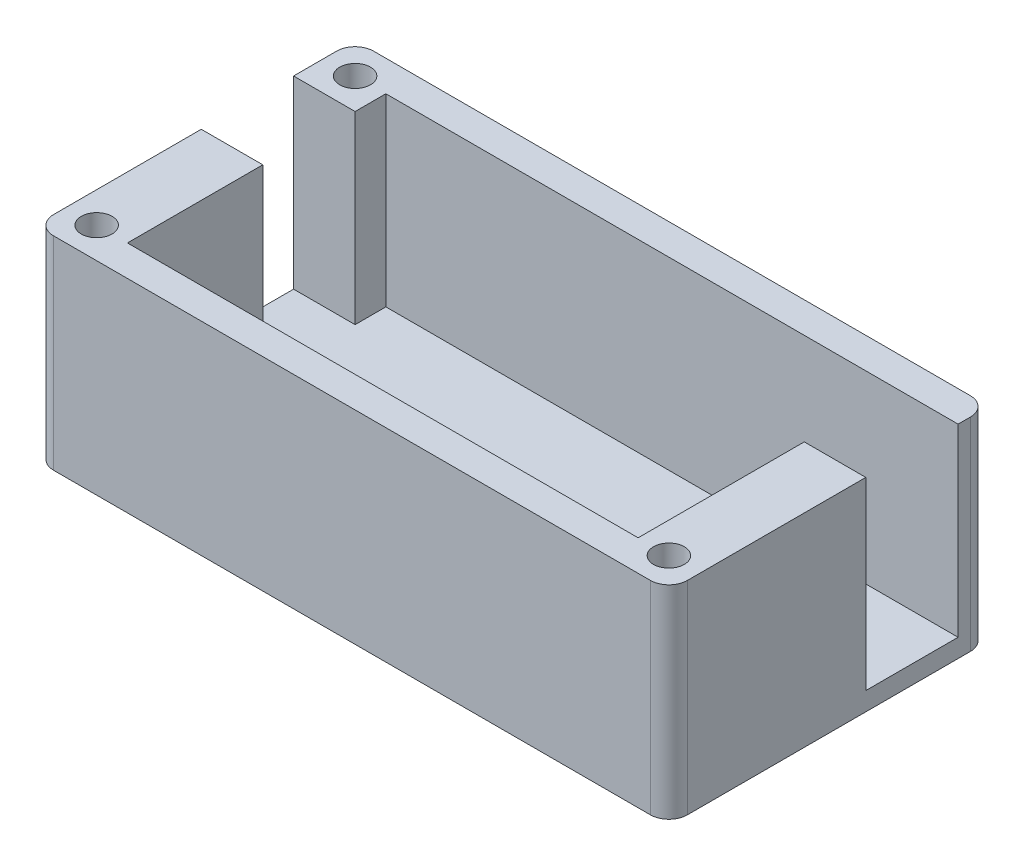
SolidWorks part; units mm, degrees
ref_plane "Front Plane" through (0, 0, 0) normal (0, 0, 1) x (1, 0, 0)
ref_plane "Top Plane" through (0, 0, 0) normal (0, 1, 0) x (1, 0, 0)
ref_plane "Right Plane" through (0, 0, 0) normal (1, 0, 0) x (0, 0, -1)
sketch "Sketch1" plane through (0, 0, 0) normal (0, 1, 0) x (1, 0, 0)
  line L1 (-41.5, -21) -> (41.5, -21)
  line L2 (-41.5, -21) -> (-41.5, 21)
  line L3 (-41.5, 21) -> (41.5, 21)
  line L4 (41.5, -21) -> (41.5, 21)
  line L5 (-41.5, -21) -> (41.5, 21) construction
  line L6 (-41.5, 21) -> (41.5, -21) construction
  line L7 (-51.5, -26) -> (51.5, -26)
  line L8 (-51.5, -26) -> (-51.5, 26)
  line L9 (-51.5, 26) -> (51.5, 26)
  line L10 (51.5, -26) -> (51.5, 26)
  line L11 (-51.5, -26) -> (51.5, 26) construction
  line L12 (-51.5, 26) -> (51.5, -26) construction
  point P0 (0, 0)
  point P6 (0, 0)
  point P11 (0, 0)
  point P16 (-52.194, 18.3459)
  dimension "D1" = 42
  dimension "D2" = 83
  dimension "D3" = 5
  dimension "D4" = 10
extrude "Boss-Extrude1" add sketch "Sketch1" along normal blind 30
sketch "Sketch2" plane through (0, 0, 0) normal (0, -1, 0) x (1, 0, 0)
  line L0 (51.5, 26) -> (51.5, -26) construction
  line L1 (51.5, -26) -> (-51.5, -26) construction
  line L2 (-51.5, -26) -> (-51.5, 26) construction
  line L3 (-51.5, 26) -> (51.5, 26) construction
  line L4 (51.5, 26) -> (51.5, -26)
  line L5 (51.5, -26) -> (-51.5, -26)
  line L6 (-51.5, -26) -> (-51.5, 26)
  line L7 (-51.5, 26) -> (51.5, 26)
extrude "Boss-Extrude2" add sketch "Sketch2" along normal blind 3
sketch "Sketch3" plane through (0, 30, 0) normal (0, 1, 0) x (1, 0, 0)
  line L0 (51.5, -26) -> (51.5, 26) construction
  line L1 (41.5, 21) -> (51.5, 21)
  line L2 (41.5, 21) -> (41.5, 6)
  line L3 (41.5, 6) -> (51.5, 6)
  line L4 (51.5, 21) -> (51.5, 6)
  line L5 (-41.5, 21) -> (-41.5, -21) construction
  line L6 (-41.5, 1) -> (-51.5, 1)
  line L7 (-41.5, 1) -> (-41.5, 16)
  line L8 (-41.5, 16) -> (-51.5, 16)
  line L9 (-51.5, 1) -> (-51.5, 16)
  line L10 (-51.5, 26) -> (-51.5, -26) construction
  line L11 (51.5, 26) -> (-51.5, 26) construction
  dimension "D1" = 10
  dimension "D2" = 15
  dimension "D3" = 15
extrude "Cut-Extrude1" cut sketch "Sketch3" against normal up to surface (30 mm away) up to face at (0, 0, 0)
hole_wizard "Ø5.0mm Dowel Hole1" positions "Sketch4" profile "Sketch6" hole size "Ø5.0" standard "ANSI Metric"
sketch "Sketch4" plane through (0, 30, 0) normal (0, 1, 0) x (1, 0, 0)
  line L0 (-51.5, 26) -> (-51.5, 16) construction
  line L1 (-51.5, 1) -> (-51.5, -26) construction
  line L2 (-51.5, -26) -> (51.5, -26) construction
  line L3 (51.5, 26) -> (-51.5, 26) construction
  line L4 (51.5, -26) -> (51.5, 6) construction
  point P0 (-46.5, 21)
  point P2 (46.5, -21)
  point P4 (-46.5, -21)
  dimension "D1" = 5
  dimension "D2" = 5
  dimension "D3" = 5
  dimension "D4" = 5
  dimension "D5" = 5
  dimension "D6" = 5
sketch "Sketch6" plane through (-46.5, 30, -21) normal (1, 0, 0) x (0, 0, 1)
  line L0 (0, 0) -> (0, 11.5022)
  line L1 (0, 11.5022) -> (2.5, 10)
  line L2 (2.5, 10) -> (2.5, 0)
  line L5 (2.5, 0) -> (0, 0)
  line L10 (0, 11.5022) -> (-2.5, 10) construction
  line L11 (0, -6.35) -> (0, 107.95) construction
  dimension "Hole Dia." = 5
  dimension "Hole Depth" = 10
  dimension "Drill Angle" = 118
fillet "Fillet1" radius 3 4 edges at (51.5, 13.5, -26) (51.5, 13.5, 26) (-51.5, 13.5, 26) (-51.5, 13.5, -26)
